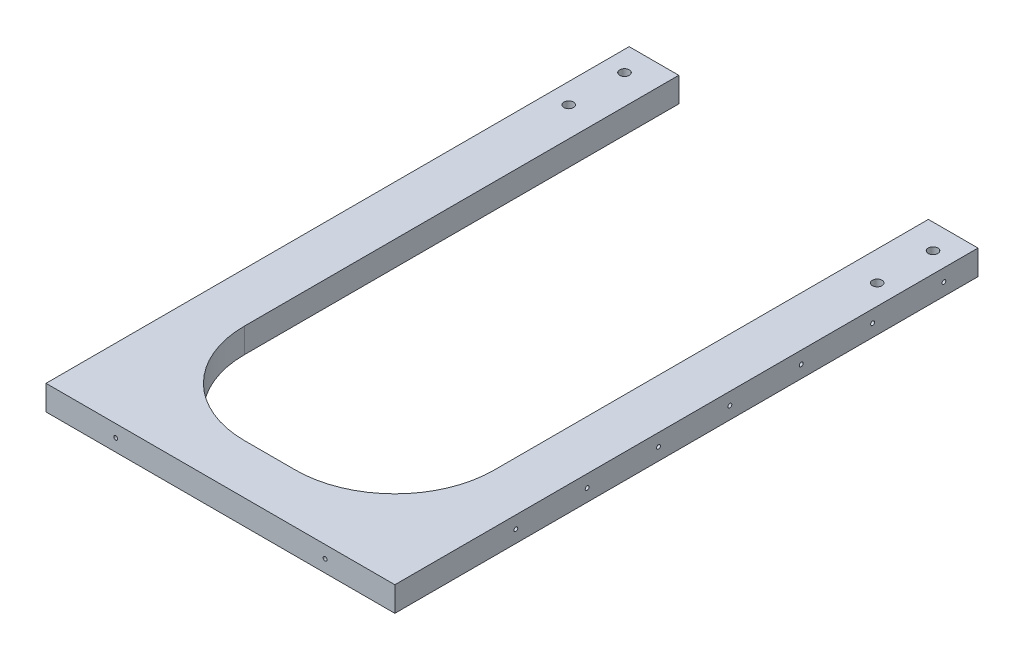
SolidWorks part; units mm, degrees
material "MDF"
ref_plane "Front" through (0, 0, 0) normal (0, 0, 1) x (1, 0, 0)
ref_plane "Top" through (0, 0, 0) normal (0, 1, 0) x (1, 0, 0)
ref_plane "Right" through (0, 0, 0) normal (1, 0, 0) x (0, 0, -1)
sketch "Sketch1" plane through (0, 0, 0) normal (0, 0, 1) x (1, 0, 0)
  line L0 (-271.672, -233.3625) -> (-271.672, -196.215) construction
  line L1 (-271.672, -193.04) -> (-93.1354, -193.04)
  line L2 (-271.672, -193.04) -> (-271.672, -180.34)
  line L3 (-271.672, -180.34) -> (-93.1354, -180.34)
  line L4 (-93.1354, -193.04) -> (-93.1354, -180.34)
  line L6 (-93.1354, -233.3625) -> (-93.1354, -196.215) construction
  line L7 (-93.1354, -196.215) -> (-271.672, -196.215) construction
  dimension "D1" = 12.7
  dimension "D2" = 3.175
extrude "Boss-Extrude1" add sketch "Sketch1" along normal up to surface (342.9 mm away)
sketch "Sketch2" plane through (0, -193.04, 0) normal (0, -1, 0) x (1, 0, 0)
  line L0 (-118.5354, 317.5) -> (-246.272, 317.5)
  line L1 (-246.272, 317.5) -> (-246.272, 25.4)
  line L2 (-246.272, 25.4) -> (-118.5354, 25.4)
  line L3 (-118.5354, 25.4) -> (-118.5354, 317.5)
  line L4 (-93.1354, 342.9) -> (-271.672, 342.9)
  line L5 (-271.672, 342.9) -> (-271.672, 0)
  line L6 (-271.672, 0) -> (-93.1354, 0)
  line L7 (-93.1354, 0) -> (-93.1354, 342.9)
  line L8 (-93.1354, 342.9) -> (-271.672, 342.9) construction
  line L9 (-271.672, 342.9) -> (-271.672, 0) construction
  line L10 (-271.672, 0) -> (-93.1354, 0) construction
  line L11 (-93.1354, 0) -> (-93.1354, 342.9) construction
  dimension "D1" = 0
  dimension "D2" = 25.4
extrude "Cut-Extrude1" cut sketch "Sketch2" against normal up to next
fillet "Fillet1" radius 50.8 4 edges at (-246.272, -186.69, 317.5) (-118.5354, -186.69, 317.5) (-118.5354, -186.69, 25.4) (-246.272, -186.69, 25.4)
hole_wizard "15/64 (0.23438) Diameter Hole2" positions "Sketch5" profile "Sketch6" hole size "15/64" standard "ANSI Inch"
sketch "Sketch5" plane through (-182.4037, 1936.854, -6.35) normal (0, 0, -1) x (1, 0, 0)
  point P0 (-262.8265, 2051.0885)
  point P3 (-262.8265, 2014.0687)
  point P6 (-262.8265, 1977.0488)
  point P9 (-98.7933, 2115.9598)
  point P12 (-98.7933, 2151.1665)
  point P15 (-44.6341, 2123.544)
  point P18 (0, 2123.544)
  point P21 (44.6341, 2123.544)
sketch "Sketch6" plane through (-445.2302, -114.2346, -6.35) normal (1, 0, 0) x (0, 1, 0)
  line L0 (0, 0) -> (0, 14.4885)
  line L1 (0, 14.4885) -> (2.9766, 12.7)
  line L2 (2.9766, 12.7) -> (2.9766, 0)
  line L3 (2.9766, 0) -> (0, 0)
  line L4 (0, 14.4885) -> (-2.9766, 12.7) construction
  line L5 (0, -6.35) -> (0, 107.95) construction
  dimension "Hole Dia." = 5.9533
  dimension "Hole Depth" = 12.7
  dimension "Drill Angle" = 118
hole_wizard "5/64 (0.07813) Diameter Hole1" positions "Sketch7" profile "Sketch8" hole size "5/64" standard "ANSI Inch"
sketch "Sketch7" plane through (-182.4037, 1936.854, 361.95) normal (0, 0, 1) x (-1, 0, 0)
  line L23 (262.8265, 2088.1084) -> (262.8265, 2038.7486)
  line L24 (262.8265, 2038.7486) -> (262.8265, 1989.3888)
  line L25 (262.8265, 1989.3888) -> (262.8265, 2038.7486)
  line L26 (262.8265, 2038.7486) -> (262.8265, 1989.3888)
  line L27 (262.8265, 1989.3888) -> (262.8265, 1940.029)
  line L33 (98.7933, 2170.2165) -> (98.7933, 2131.8519)
  line L35 (98.7933, 2131.8519) -> (98.7933, 2093.4873)
  line L36 (98.7933, 2093.4873) -> (98.7933, 2055.1227)
  line L37 (98.7933, 2055.1227) -> (98.7933, 2016.7581)
  line L38 (98.7933, 2016.7581) -> (98.7933, 1978.3935)
  line L39 (98.7933, 1978.3935) -> (98.7933, 1940.029)
  line L44 (89.2683, 2123.544) -> (53.561, 2123.544)
  line L46 (53.561, 2123.544) -> (17.8537, 2123.544)
  line L48 (-17.8537, 2123.544) -> (-53.561, 2123.544)
  line L49 (-53.561, 2123.544) -> (-89.2683, 2123.544)
  line L53 (0, 2170.2165) -> (0.2777, 1940.029) construction
  line L55 (-98.3301, 1978.1557) -> (-98.2375, 1939.7912)
  line L56 (-98.4227, 2016.5202) -> (-98.3301, 1978.1557)
  line L57 (-98.5153, 2054.8846) -> (-98.4227, 2016.5202)
  line L58 (-98.6078, 2093.2491) -> (-98.5153, 2054.8846)
  line L59 (-98.7004, 2131.6136) -> (-98.6078, 2093.2491)
  line L60 (-98.793, 2169.978) -> (-98.7004, 2131.6136)
  line L61 (-262.3894, 1988.755) -> (-262.2702, 1939.3954)
  line L62 (-262.5085, 2038.1147) -> (-262.3894, 1988.755)
  line L63 (-262.3894, 1988.755) -> (-262.5085, 2038.1147)
  line L64 (-262.5085, 2038.1147) -> (-262.3894, 1988.755)
  line L65 (-262.6276, 2087.4744) -> (-262.5085, 2038.1147)
  point P61 (262.8265, 2038.7486)
  point P63 (262.8265, 1989.3888)
  point P71 (262.8265, 1964.7089)
  point P75 (262.8265, 2014.0687)
  point P79 (262.8265, 2063.4285)
  point P95 (98.7933, 2131.8519)
  point P99 (98.7933, 2093.4873)
  point P100 (98.7933, 2055.1227)
  point P102 (98.7933, 2016.7581)
  point P103 (98.7933, 1978.3935)
  point P126 (53.561, 2123.544)
  point P134 (-53.561, 2123.544)
  point P162 (-98.3301, 1978.1557)
  point P163 (-98.4227, 2016.5202)
  point P164 (-98.5153, 2054.8846)
  point P165 (-98.6078, 2093.2491)
  point P166 (-98.7004, 2131.6136)
  point P167 (-262.568, 2062.7945)
  point P168 (-262.4489, 2013.4349)
  point P169 (-262.3298, 1964.0752)
  point P170 (-262.3894, 1988.755)
  point P171 (-262.5085, 2038.1147)
sketch "Sketch8" plane through (80.1047, -101.2608, 361.95) normal (1, 0, 0) x (0, -1, 0)
  line L0 (0, 0) -> (0, 38.6962)
  line L1 (0, 38.6962) -> (0.9923, 38.1)
  line L2 (0.9923, 38.1) -> (0.9923, 4.7024)
  line L3 (0.9923, 4.7024) -> (5.08, 0)
  line L4 (5.08, 0) -> (0, 0)
  line L5 (-0.9923, 4.7024) -> (-5.08, 0) construction
  line L6 (0, 38.6962) -> (-0.9923, 38.1) construction
  line L7 (0, -6.35) -> (0, 107.95) construction
  dimension "Hole Dia." = 1.9845
  dimension "Hole Depth" = 38.1
  dimension "Near C'Sink Dia." = 10.16
  dimension "Near C'Sink Angle" = 82
  dimension "Drill Angle" = 118
hole_wizard "5/64 (0.07813) Diameter Hole2" positions "Sketch9" profile "Sketch10" hole size "5/64" standard "ANSI Inch"
sketch "Sketch9" plane through (-271.672, 0, 0) normal (-1, 0, 0) x (0, 0, 1)
  point P0 (280.9875, -186.69)
  point P3 (244.475, -186.69)
  point P6 (207.9625, -186.69)
  point P9 (171.45, -186.69)
  point P12 (134.9375, -186.69)
  point P15 (98.425, -186.69)
  point P18 (61.9125, -186.69)
sketch "Sketch10" plane through (-271.672, -186.69, 280.9875) normal (0, 1, 0) x (0, 0, 1)
  line L0 (0, 0) -> (0, 19.6462)
  line L1 (0, 19.6462) -> (0.9923, 19.05)
  line L2 (0.9923, 19.05) -> (0.9923, 0)
  line L5 (0.9923, 0) -> (0, 0)
  line L10 (0, 19.6462) -> (-0.9923, 19.05) construction
  line L11 (0, -6.35) -> (0, 107.95) construction
  dimension "Hole Dia." = 1.9845
  dimension "Hole Depth" = 19.05
  dimension "Drill Angle" = 118
ref_plane "Plane1" through (-182.4037, 0, 0) normal (-1, 0, 0) x (0, 0, 1)
mirror "Mirror1" about plane through (-182.4037, 0, 0) normal (-1, 0, 0) of "5/64 (0.07813) Diameter Hole2"
sketch "Sketch11" plane through (0, -193.04, 0) normal (0, -1, 0) x (1, 0, 0)
  line L0 (-271.672, 342.9) -> (-271.672, 0) construction
  line L1 (-93.1354, 0) -> (-271.672, 0)
  line L2 (-93.1354, 0) -> (-93.1354, 44.45)
  line L3 (-93.1354, 44.45) -> (-271.672, 44.45)
  line L4 (-271.672, 0) -> (-271.672, 44.45)
  dimension "D1" = 44.45
extrude "Cut-Extrude2" cut sketch "Sketch11" against normal up to next
sketch "Sketch12" plane through (0, -193.04, 0) normal (0, -1, 0) x (1, 0, 0)
  line L0 (-235.1278, 44.45) -> (-271.672, 44.45) construction
  line L1 (-118.5354, 76.2) -> (-246.272, 76.2)
  line L2 (-118.5354, 76.2) -> (-118.5354, 44.45)
  line L3 (-118.5354, 44.45) -> (-246.272, 44.45)
  line L4 (-246.272, 76.2) -> (-246.272, 44.45)
  line L5 (-246.272, 266.7) -> (-246.272, 76.2) construction
extrude "Cut-Extrude3" cut sketch "Sketch12" against normal up to next
chamfer "Chamfer1" [suppressed] distance 12.7 angle 45
hole_wizard "#8 Clearance Hole1" positions "Sketch13" profile "Sketch14" hole size "#8" standard "ANSI Inch" end condition through all
sketch "Sketch13" plane through (0, -193.04, 0) normal (0, -1, 0) x (-1, 0, 0)
  line L0 (182.4037, -342.9) -> (182.4037, -317.5) construction
  line L1 (271.672, -342.9) -> (93.1354, -342.9) construction
  line L2 (169.3354, -317.5) -> (195.472, -317.5) construction
  circle A0 centre (261.3533, -57.15) radius 2.4574 construction
  point P0 (261.3533, -85.725)
  point P4 (261.3533, -57.15)
  point P17 (103.4542, -57.15)
  point P18 (103.4542, -85.725)
sketch "Sketch14" plane through (-261.3533, -193.04, 85.725) normal (1, 0, 0) x (0, 0, -1)
  line L0 (0, 0) -> (0, 12.7)
  line L1 (0, 12.7) -> (2.4574, 12.7)
  line L2 (2.4574, 12.7) -> (2.4574, 0)
  line L5 (2.4574, 0) -> (0, 0)
  line L11 (0, -6.35) -> (0, 107.95) construction
  dimension "Thru Hole Dia." = 4.9149
  dimension "Thru Hole Depth" = 12.7
